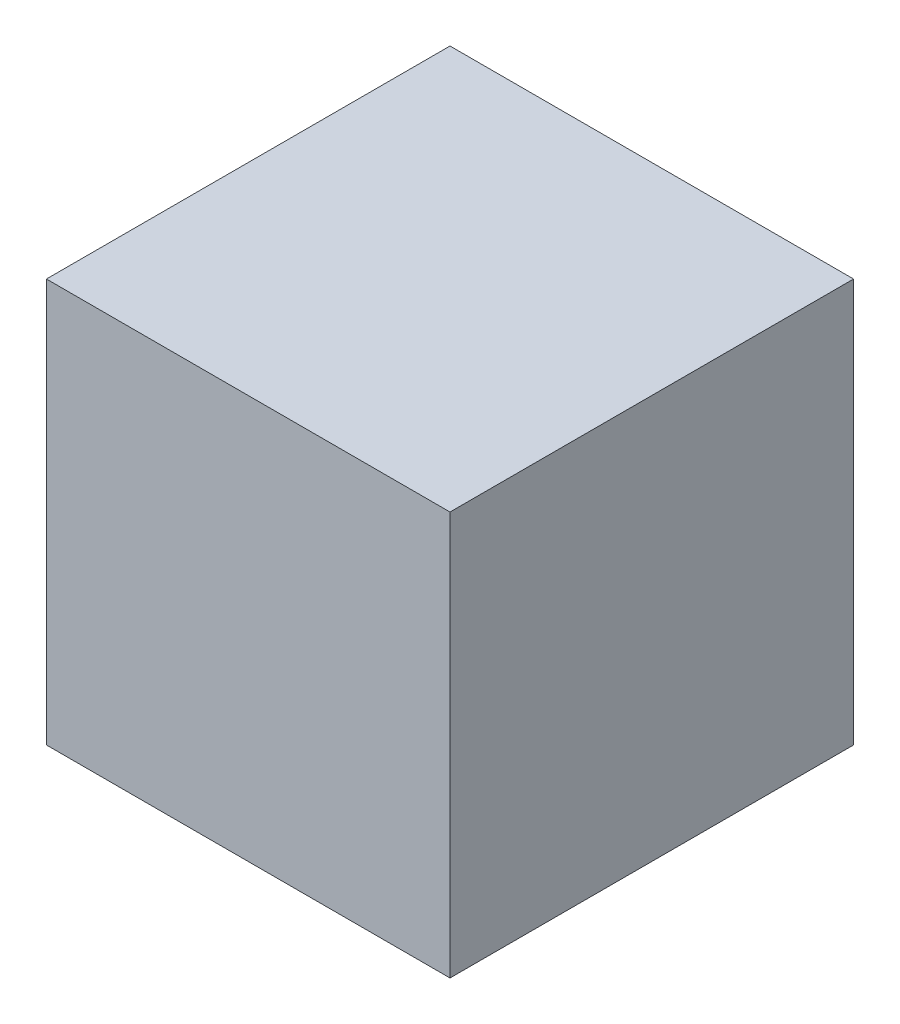
SolidWorks part; units mm, degrees
ref_plane "Front Plane" through (0, 0, 0) normal (0, 0, 1) x (1, 0, 0)
ref_plane "Top Plane" through (0, 0, 0) normal (0, 1, 0) x (1, 0, 0)
ref_plane "Right Plane" through (0, 0, 0) normal (1, 0, 0) x (0, 0, -1)
sketch "xz bounding" plane through (0, 0, 0) normal (0, 1, 0) x (1, 0, 0)
  line L0 (0, 0) -> (0, 1219.2)
  line L1 (304.8, -304.8) -> (-304.8, -304.8)
  line L2 (304.8, -304.8) -> (304.8, 304.8)
  line L3 (304.8, 304.8) -> (-304.8, 304.8)
  line L4 (-304.8, -304.8) -> (-304.8, 304.8)
  line L5 (304.8, -304.8) -> (-304.8, 304.8) construction
  line L6 (304.8, 304.8) -> (-304.8, -304.8) construction
  line L7 (-609.6, 2489.2) -> (609.6, 2489.2)
  line L8 (-609.6, 2489.2) -> (-609.6, -304.8)
  line L9 (-609.6, -304.8) -> (609.6, -304.8)
  line L10 (609.6, 2489.2) -> (609.6, -304.8)
  line L11 (0, 1219.2) -> (661.1202, 2489.2) construction
  line L12 (0, 1219.2) -> (-661.1202, 2489.2) construction
  point P0 (0, 0)
  point P10 (415.3891, 1688.6172)
  point P11 (0, -304.8)
  point P16 (835.2368, 2823.6749)
  point P17 (0, 0)
  point P18 (0, 0)
  dimension "D1" = 609.6
  dimension "D2" = 2794
  dimension "D3" = 1219.2
  dimension "D4" = 1219.2
  dimension "D5" = 55
  dimension "D6" = 1270
ref_plane "Plane1" through (0, 0, -2489.2) normal (0, 0, 1) x (1, 0, 0)
sketch "zy bounding" plane through (0, 0, 0) normal (1, 0, 0) x (0, 0, -1)
  line L0 (1219.2, 0) -> (2489.2, 957.0136)
  line L1 (1219.2, 0) -> (2489.2, 44.3494)
  line L2 (2489.2, 670.56) -> (2489.2, -670.56) construction
  line L3 (727.2322, 0) -> (-727.2322, 0) construction
  line L5 (-304.8, 609.6) -> (304.8, 609.6)
  line L6 (-304.8, 609.6) -> (-304.8, 0)
  line L7 (-304.8, 0) -> (304.8, 0)
  line L8 (304.8, 609.6) -> (304.8, 0)
  point P3 (0, 0)
  point P5 (0, 0)
  dimension "D1" = 35
  dimension "D2" = 2
sketch "projected person" plane through (0, 0, -2489.2) normal (0, 0, 1) x (1, 0, 0)
  line L1 (-200, -711.2) -> (200, -711.2)
  line L2 (-200, -711.2) -> (-200, 888.8)
  line L3 (-200, 888.8) -> (200, 888.8)
  line L4 (200, -711.2) -> (200, 888.8)
  line L5 (-661.1202, 957.0136) -> (661.1202, 957.0136)
  line L6 (-661.1202, 957.0136) -> (-661.1202, 44.3494)
  line L7 (-661.1202, 44.3494) -> (661.1202, 44.3494)
  line L8 (661.1202, 957.0136) -> (661.1202, 44.3494)
  point P4 (0, -711.2)
  dimension "D1" = 400
  dimension "D2" = 1600
  dimension "D3" = 711.2
extrude "Boss-Extrude1" add sketch "zy bounding" along normal mid plane 609.6 contours L8 L5 L6 L7
